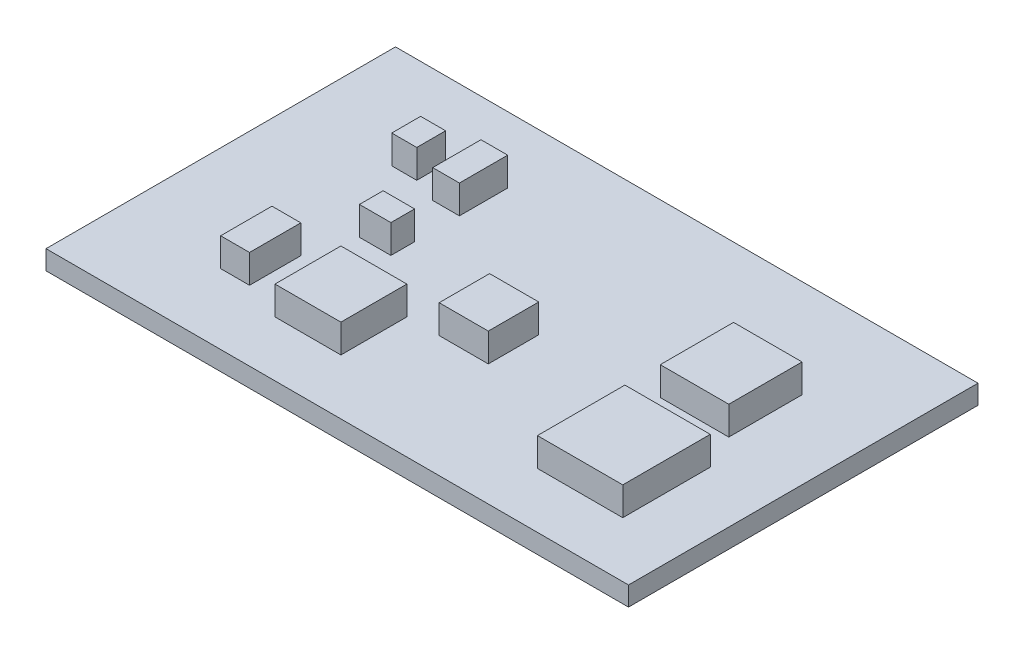
SolidWorks part; units mm, degrees
ref_plane "Front Plane" through (0, 0, 0) normal (0, 0, 1) x (1, 0, 0)
ref_plane "Top Plane" through (0, 0, 0) normal (0, 1, 0) x (1, 0, 0)
ref_plane "Right Plane" through (0, 0, 0) normal (1, 0, 0) x (0, 0, -1)
sketch "Sketch1" plane through (0, 0, 0) normal (0, 1, 0) x (1, 0, 0)
  line L1 (-16.375, 9.825) -> (16.375, 9.825)
  line L2 (-16.375, 9.825) -> (-16.375, -9.825)
  line L3 (-16.375, -9.825) -> (16.375, -9.825)
  line L4 (16.375, 9.825) -> (16.375, -9.825)
  line L5 (-16.375, 9.825) -> (16.375, -9.825) construction
  line L6 (-16.375, -9.825) -> (16.375, 9.825) construction
  point P0 (0, 0)
  dimension "D1" = 19.65
  dimension "D2" = 32.75
extrude "Boss-Extrude1" add sketch "Sketch1" along normal blind 1.08
sketch "Sketch2" plane through (0, 1.08, 0) normal (0, 1, 0) x (1, 0, 0)
  line L1 (-10.686, 5.549) -> (-9.2806, 5.549)
  line L2 (-10.686, 5.549) -> (-10.686, 3.9255)
  line L3 (-10.686, 3.9255) -> (-9.2806, 3.9255)
  line L4 (-9.2806, 5.549) -> (-9.2806, 3.9255)
  line L5 (-7.851, 6.1063) -> (-6.3486, 6.1063)
  line L6 (-7.851, 6.1063) -> (-7.851, 3.3924)
  line L7 (-7.851, 3.3924) -> (-6.3486, 3.3924)
  line L8 (-6.3486, 6.1063) -> (-6.3486, 3.3924)
  line L9 (-10.4922, -3.0047) -> (-8.8687, -3.0047)
  line L10 (-10.4922, -3.0047) -> (-10.4922, -5.8882)
  line L11 (-10.4922, -5.8882) -> (-8.8687, -5.8882)
  line L12 (-8.8687, -3.0047) -> (-8.8687, -5.8882)
  line L13 (-6.6152, -3.0047) -> (-2.9078, -3.0047)
  line L14 (-6.6152, -3.0047) -> (-6.6152, -6.7121)
  line L15 (-6.6152, -6.7121) -> (-2.9078, -6.7121)
  line L16 (-2.9078, -3.0047) -> (-2.9078, -6.7121)
  line L17 (-1.0904, -0.1696) -> (1.672, -0.1696)
  line L18 (-1.0904, -0.1696) -> (-1.0904, -3.0047)
  line L19 (-1.0904, -3.0047) -> (1.672, -3.0047)
  line L20 (1.672, -0.1696) -> (1.672, -3.0047)
  line L21 (8.1417, -1.7931) -> (12.9396, -1.7931)
  line L22 (8.1417, -1.7931) -> (8.1417, -6.7121)
  line L23 (8.1417, -6.7121) -> (12.9396, -6.7121)
  line L24 (12.9396, -1.7931) -> (12.9396, -6.7121)
  line L25 (8.1417, 4.3132) -> (11.9945, 4.3132)
  line L26 (8.1417, 4.3132) -> (8.1417, 0.1939)
  line L27 (8.1417, 0.1939) -> (11.9945, 0.1939)
  line L28 (11.9945, 4.3132) -> (11.9945, 0.1939)
  line L29 (-8.1175, 0.8723) -> (-6.3486, 0.8723)
  line L30 (-8.1175, 0.8723) -> (-8.1175, -0.4604)
  line L31 (-8.1175, -0.4604) -> (-6.3486, -0.4604)
  line L32 (-6.3486, 0.8723) -> (-6.3486, -0.4604)
extrude "Boss-Extrude2" add sketch "Sketch2" along normal blind 1.6
sketch "Sketch3" plane through (0, 0, 0) normal (0, -1, 0) x (1, 0, 0)
  line L1 (-4.2647, 4.4101) -> (2.5443, 4.4101)
  line L2 (-4.2647, 4.4101) -> (-4.2647, -2.5685)
  line L3 (-4.2647, -2.5685) -> (2.5443, -2.5685)
  line L4 (2.5443, 4.4101) -> (2.5443, -2.5685)
  line L5 (-12.6488, -4.2163) -> (-9.4502, -4.2163)
  line L6 (-12.6488, -4.2163) -> (-12.6488, -5.6217)
  line L7 (-12.6488, -5.6217) -> (-9.4502, -5.6217)
  line L8 (-9.4502, -4.2163) -> (-9.4502, -5.6217)
  line L9 (-8.9898, -4.2163) -> (-6.2032, -4.2163)
  line L10 (-8.9898, -4.2163) -> (-8.9898, -5.6217)
  line L11 (-8.9898, -5.6217) -> (-6.2032, -5.6217)
  line L12 (-6.2032, -4.2163) -> (-6.2032, -5.6217)
  line L13 (-6.6394, 6.1548) -> (-9.7168, 6.1548)
  line L14 (-6.6394, 6.1548) -> (-6.6394, 4.6767)
  line L15 (-6.6394, 4.6767) -> (-9.7168, 4.6767)
  line L16 (-9.7168, 6.1548) -> (-9.7168, 4.6767)
  line L17 (-10.1287, 6.1548) -> (-13.2546, 6.1548)
  line L18 (-10.1287, 6.1548) -> (-10.1287, 4.6767)
  line L19 (-10.1287, 4.6767) -> (-13.2546, 4.6767)
  line L20 (-13.2546, 6.1548) -> (-13.2546, 4.6767)
extrude "Boss-Extrude3" add sketch "Sketch3" along normal blind 1.45
